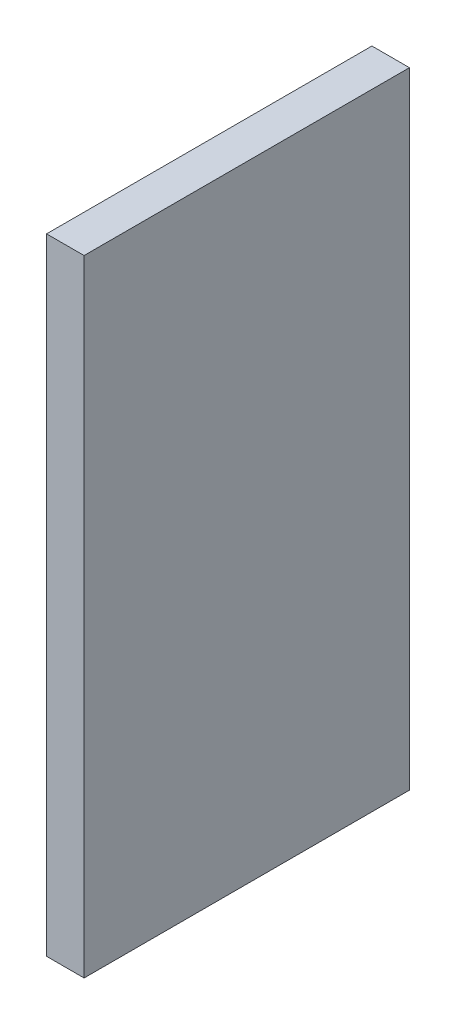
SolidWorks part; units mm, degrees
material "Balsa"
ref_plane "Alzado" through (0, 0, 0) normal (0, 0, 1) x (1, 0, 0)
ref_plane "Planta" through (0, 0, 0) normal (0, 1, 0) x (1, 0, 0)
ref_plane "Vista lateral" through (0, 0, 0) normal (1, 0, 0) x (0, 0, -1)
sketch "Croquis1" plane through (0, 0, 0) normal (1, 0, 0) x (0, 0, -1)
  line L1 (0, 0) -> (-26, 0)
  line L2 (0, 0) -> (0, 50)
  line L3 (0, 50) -> (-26, 50)
  line L4 (-26, 0) -> (-26, 50)
  dimension "D1" = 26
  dimension "D2" = 50
extrude "Saliente-Extruir1" add sketch "Croquis1" along normal blind 3
